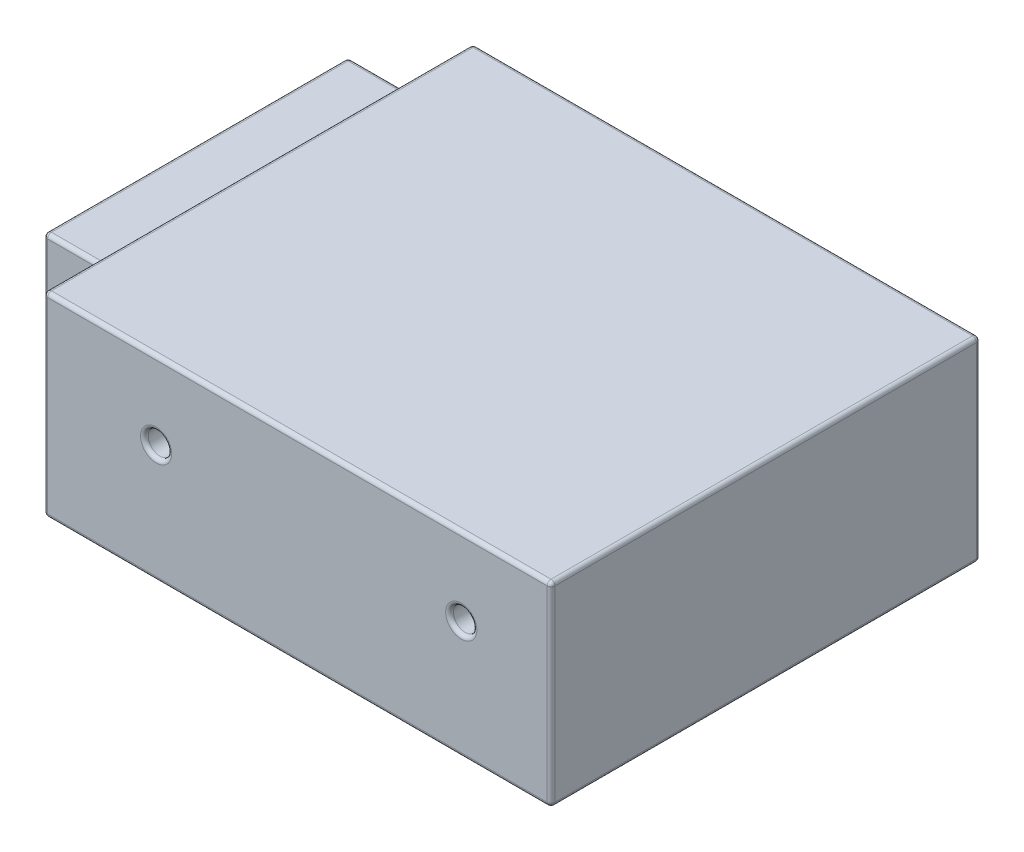
SolidWorks part; units mm, degrees
ref_plane "Front Plane" through (0, 0, 0) normal (0, 0, 1) x (1, 0, 0)
ref_plane "Top Plane" through (0, 0, 0) normal (0, 1, 0) x (1, 0, 0)
ref_plane "Right Plane" through (0, 0, 0) normal (1, 0, 0) x (0, 0, -1)
sketch "Sketch1" plane through (0, 0, 0) normal (0, 1, 0) x (1, 0, 0)
  line L1 (-32.5, -27.5) -> (32.5, -27.5)
  line L2 (-32.5, -27.5) -> (-32.5, 27.5)
  line L3 (-32.5, 27.5) -> (32.5, 27.5)
  line L4 (32.5, -27.5) -> (32.5, 27.5)
  line L5 (-32.5, -27.5) -> (32.5, 27.5) construction
  line L6 (-32.5, 27.5) -> (32.5, -27.5) construction
  point P0 (0, 0)
  dimension "D1" = 65
  dimension "D2" = 55
extrude "Boss-Extrude1" add sketch "Sketch1" along normal blind 25
sketch "Sketch2" plane through (0, 0, 0) normal (0, -1, 0) x (1, 0, 0)
  line L0 (-32.5, 27.5) -> (32.5, 27.5) construction
  line L1 (32.5, 27.5) -> (32.5, -27.5) construction
  circle A0 centre (17.85, 2.25) radius 1.5
  circle A1 centre (-21.25, 2.25) radius 1.5
  dimension "D1" = 3
  dimension "D2" = 25.25
  dimension "D3" = 14.65
  dimension "D4" = 39.1
extrude "Cut-Extrude1" cut sketch "Sketch2" against normal blind 5
sketch "Sketch3" plane through (0, 0, 27.5) normal (0, 0, 1) x (1, 0, 0)
  line L0 (-32.5, 25) -> (32.5, 25) construction
  line L1 (32.5, 25) -> (32.5, 0) construction
  line L2 (-32.5, 0) -> (32.5, 0) construction
  circle A0 centre (21, 15.1) radius 1.5
  circle A1 centre (-18.1, 15.1) radius 1.5
  dimension "D1" = 3
  dimension "D2" = 9.9
  dimension "D3" = 11.5
  dimension "D4" = 39.1
extrude "Cut-Extrude2" cut sketch "Sketch3" against normal blind 5
sketch "Sketch4" plane through (-32.5, 0, 0) normal (-1, 0, 0) x (0, 0, 1)
  line L0 (-27.5, 0) -> (27.5, 0) construction
  line L1 (-24.5, 7) -> (14.5, 7)
  line L2 (-24.5, 7) -> (-24.5, 18.5)
  line L3 (-24.5, 18.5) -> (14.5, 18.5)
  line L4 (14.5, 7) -> (14.5, 18.5)
  line L5 (27.5, 25) -> (27.5, 0) construction
  line L7 (-27.5, 25) -> (27.5, 25) construction
  line L8 (-27.5, 25) -> (-27.5, 0) construction
  dimension "D1" = 7
  dimension "D2" = 6.5
  dimension "D3" = 3
  dimension "D4" = 13
extrude "Boss-Extrude2" add sketch "Sketch4" along normal blind 13
fillet "Fillet1" radius 0.5 28 edges at (-39, 18.5, 14.5) (-39, 18.5, -24.5) (-39, 7, -24.5) (-39, 7, 14.5) (-45.5, 7, -5) (-45.5, 12.75, -24.5) (-45.5, 18.5, -5) (-45.5, 12.75, 14.5) (32.5, 12.5, -27.5) (32.5, 12.5, 27.5) (-16.6, 15.1, 27.5) (22.5, 15.1, 27.5) (0, 25, 27.5) (0, 25, -27.5) (32.5, 25, 0) (0, 0, -27.5) (0, 0, 27.5) (32.5, 0, 0) (-21.25, 0, 0.75) (17.85, 0, 0.75) (-32.5, 18.5, -5) (-32.5, 12.75, -24.5) (-32.5, 7, -5) (-32.5, 12.75, 14.5) (-32.5, 12.5, -27.5) (-32.5, 25, 0) (-32.5, 12.5, 27.5) (-32.5, 0, 0)
sketch "Sketch5" plane through (-32.5, 0, 0) normal (-1, 0, 0) x (0, 0, 1)
  line L0 (27.5, 24.5) -> (27.5, 0.5) construction
  line L1 (27, 0) -> (-27, 0) construction
  circle A0 centre (20, 11.5) radius 3.5
  dimension "D3" = 7
  dimension "D1" = 7.5
  dimension "D2" = 11.5
extrude "Boss-Extrude3" add sketch "Sketch5" along normal blind 2
